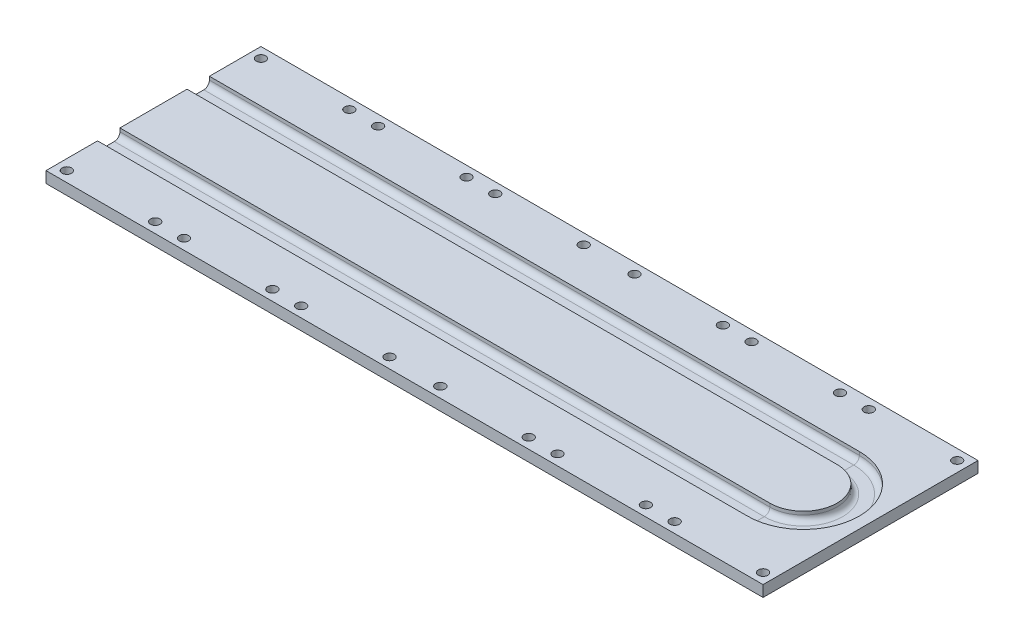
SolidWorks part; units mm, degrees
material "6061-T6 (SS)"
ref_plane "Front Plane" through (0, 0, 0) normal (0, 0, 1) x (1, 0, 0)
ref_plane "Top Plane" through (0, 0, 0) normal (0, 1, 0) x (1, 0, 0)
ref_plane "Right Plane" through (0, 0, 0) normal (1, 0, 0) x (0, 0, -1)
sketch "Sketch1" plane through (0, 0, 0) normal (0, 1, 0) x (1, 0, 0)
  line L1 (-203.5, 61) -> (203.5, 61)
  line L2 (-203.5, 61) -> (-203.5, -61)
  line L3 (-203.5, -61) -> (203.5, -61)
  line L4 (203.5, 61) -> (203.5, -61)
  line L5 (-203.5, 61) -> (203.5, -61) construction
  line L6 (-203.5, -61) -> (203.5, 61) construction
  point P0 (0, 0)
  dimension "D1" = 122
  dimension "D2" = 407
extrude "Base Plate" add sketch "Sketch1" along normal blind 6.35
sketch "Sketch2" plane through (0, 6.35, 0) normal (0, 1, 0) x (1, 0, 0)
  line L0 (147.41, 55.095) -> (147.41, -55.095) construction
  line L1 (147.41, -55.095) -> (197.595, -55.095) construction
  line L2 (197.595, -55.095) -> (197.595, 55.095) construction
  line L3 (197.595, 55.095) -> (147.41, 55.095) construction
  line L4 (203.5, -61) -> (203.5, 61) construction
  line L5 (203.5, 61) -> (-203.5, 61) construction
  line L6 (-203.5, -61) -> (203.5, -61) construction
  circle A0 centre (197.595, 55.095) radius 2.675
  circle A1 centre (197.595, -55.095) radius 2.675
  circle A2 centre (147.41, -55.095) radius 2.675
  circle A3 centre (147.41, 55.095) radius 2.675
  dimension "D4" = 5.35
  dimension "D5" = 5.35
  dimension "D6" = 5.35
  dimension "D7" = 5.35
  dimension "D1" = 5.905
  dimension "D2" = 5.905
  dimension "D3" = 5.905
  dimension "D8" = 50.185
extrude "IGBT Holes" cut sketch "Sketch2" against normal through all
pattern_linear "IGBT Holes Pattern" count 3 spacing 66.5 along (-1, 0, 0) of "IGBT Holes"
mirror "IGBT Holes Mirror" about plane through (0, 0, 0) normal (1, 0, 0) of "IGBT Holes Pattern", "IGBT Holes"
sketch "Sketch3" plane through (0, 6.35, 0) normal (0, 1, 0) x (1, 0, 0)
  line L0 (-203.5, 25.4) -> (165.4, 25.4)
  line L1 (-203.5, 61) -> (-203.5, -61) construction
  line L3 (203.5, -61) -> (203.5, 61) construction
  line L4 (165.4, 0) -> (-203.5, 0) construction
  line L5 (165.4, -25.4) -> (-203.5, -25.4)
  arc A0 (165.4, 25.4) -> (165.4, -25.4) centre (165.4, 0) cw
  dimension "D1" = 25.4
  dimension "D2" = 12.7
sketch "Sketch4" plane through (-203.5, 0, 0) normal (-1, 0, 0) x (0, 0, 1)
  line L0 (-28.575, 1.27) -> (-22.225, 1.27)
  line L1 (-61, 0) -> (61, 0) construction
  line L3 (-31.75, 4.445) -> (-31.75, 6.35)
  line L4 (-61, 6.35) -> (61, 6.35) construction
  line L5 (-31.75, 6.35) -> (-19.05, 6.35)
  line L6 (-19.05, 6.35) -> (-19.05, 4.445)
  arc A0 (-28.575, 1.27) -> (-31.75, 4.445) centre (-28.575, 4.445) cw
  arc A1 (-22.225, 1.27) -> (-19.05, 4.445) centre (-22.225, 4.445) ccw
  point P4 (-25.4, 1.27)
  dimension "D3" = 3.175
  dimension "D1" = 1.27
  dimension "D2" = 12.7
sweep "Pipe Profile" cut profiles "Sketch4" path "Sketch3"
